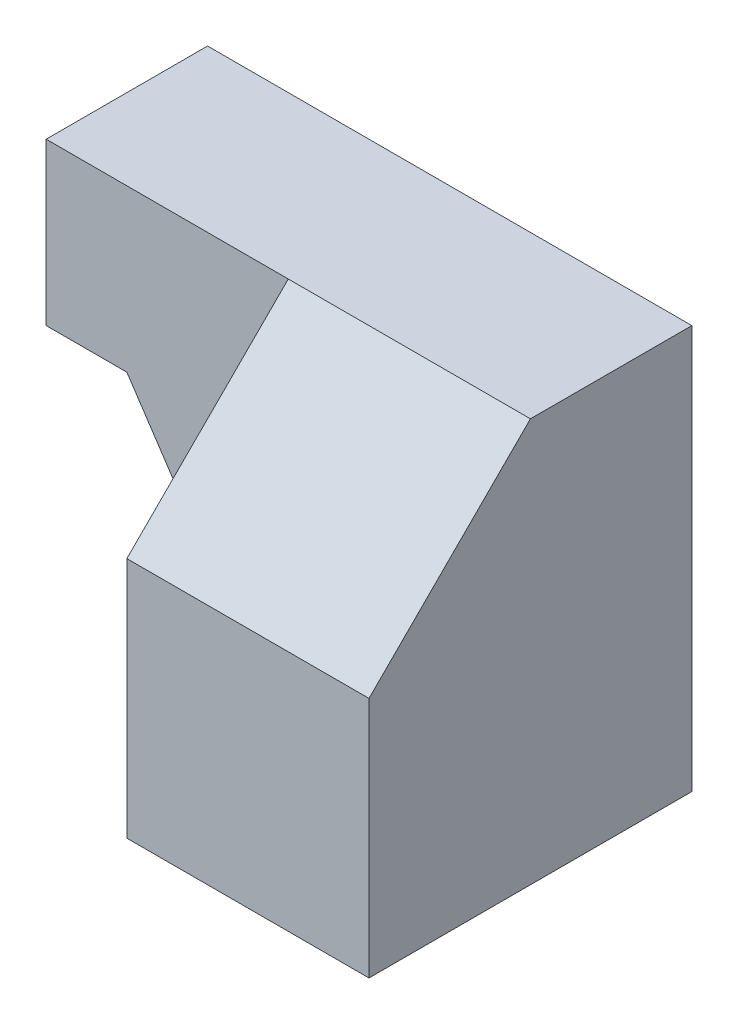
SolidWorks part; units mm, degrees
ref_plane "Front Plane" through (0, 0, 0) normal (0, 0, 1) x (1, 0, 0)
ref_plane "Top Plane" through (0, 0, 0) normal (0, 1, 0) x (1, 0, 0)
ref_plane "Right Plane" through (0, 0, 0) normal (1, 0, 0) x (0, 0, -1)
sketch "Sketch1" plane through (0, 0, 0) normal (0, 0, 1) x (1, 0, 0)
  line L0 (0, 0) -> (15, 0)
  line L1 (15, 0) -> (15, 25)
  line L2 (15, 25) -> (-15, 25)
  line L3 (-15, 25) -> (-15, 15)
  line L4 (-15, 15) -> (-10, 15)
  line L5 (-10, 15) -> (0, 0)
  dimension "D1" = 15
  dimension "D2" = 25
  dimension "D3" = 15
  dimension "D4" = 5
  dimension "D5" = 30
extrude "Boss-Extrude1" add sketch "Sketch1" along normal blind 20
sketch "Sketch2" plane through (0, 0, 20) normal (0, 0, 1) x (1, 0, 0)
  line L0 (0, 0) -> (0, 25)
  line L1 (15, 25) -> (-15, 25) construction
  line L2 (0, 25) -> (-15, 25)
  line L3 (-15, 25) -> (-15, 15)
  line L4 (-15, 15) -> (-10, 15)
  line L5 (-10, 15) -> (0, 0)
extrude "Cut-Extrude1" cut sketch "Sketch2" against normal blind 10
sketch "Sketch3" plane through (0, 0, 0) normal (-1, 0, 0) x (0, 0, 1)
  line L0 (10, 25) -> (20, 15)
  line L1 (20, 0) -> (20, 25) construction
  line L2 (20, 15) -> (20, 25)
  line L3 (20, 25) -> (10, 25)
  dimension "D1" = 10
extrude "Cut-Extrude3" cut sketch "Sketch3" against normal blind 20
